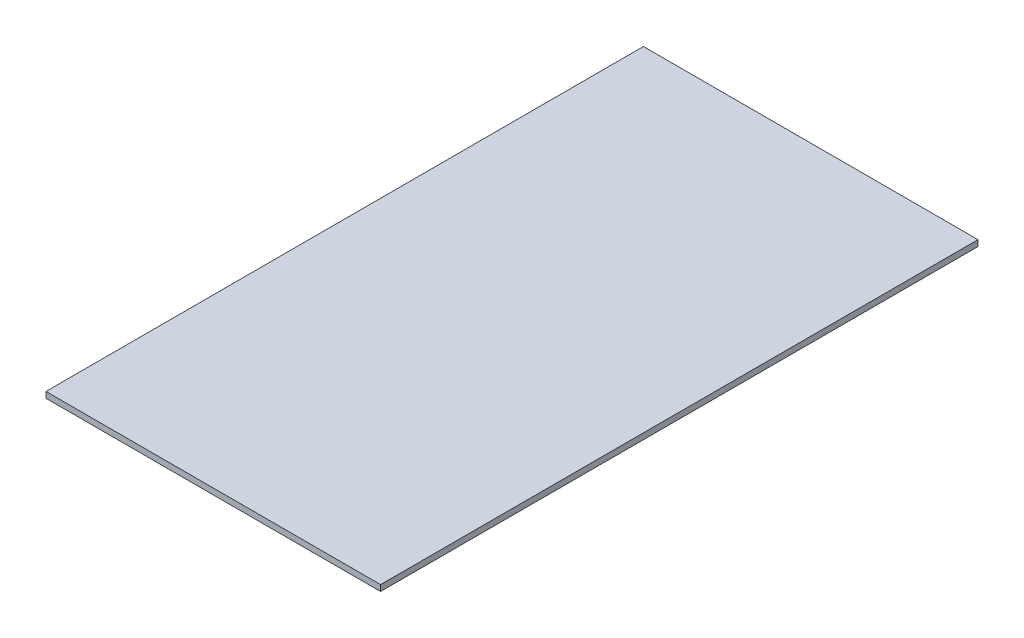
SolidWorks part; units mm, degrees
ref_plane "Front Plane" through (0, 0, 0) normal (0, 0, 1) x (1, 0, 0)
ref_plane "Top Plane" through (0, 0, 0) normal (0, 1, 0) x (1, 0, 0)
ref_plane "Right Plane" through (0, 0, 0) normal (1, 0, 0) x (0, 0, -1)
sketch "Sketch1" plane through (0, 0, 0) normal (0, 1, 0) x (1, 0, 0)
  line L1 (0, 0) -> (355.6, 0)
  line L2 (0, 0) -> (0, 635)
  line L3 (0, 635) -> (355.6, 635)
  line L4 (355.6, 0) -> (355.6, 635)
  dimension "D1" = 355.6
  dimension "D2" = 635
extrude "Boss-Extrude1" add sketch "Sketch1" along normal blind 6.35
